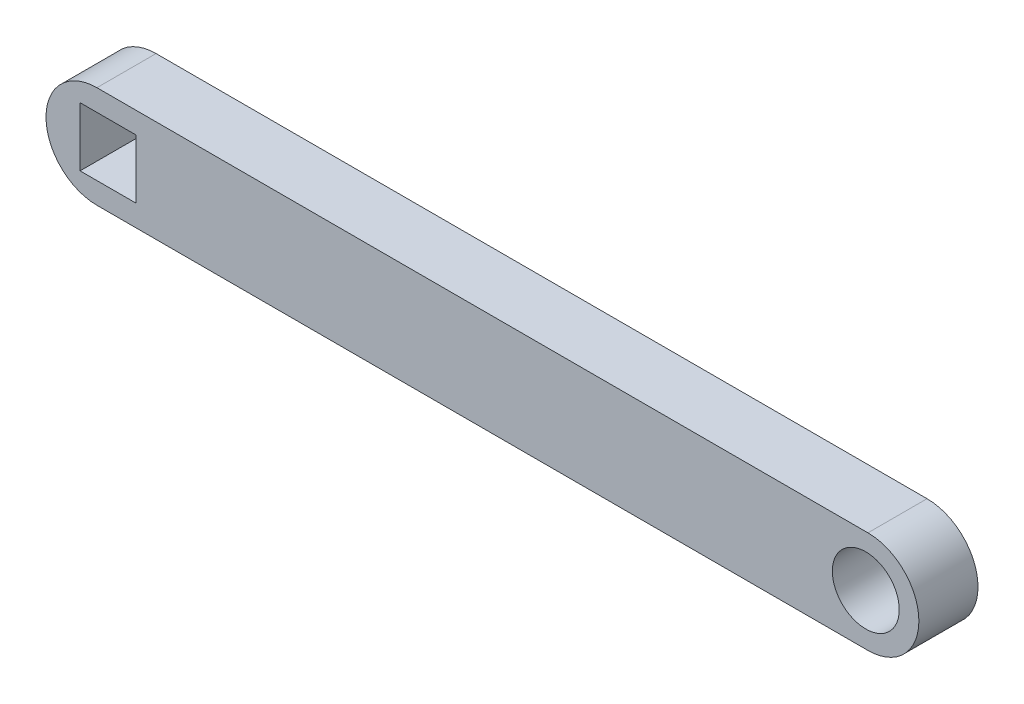
SolidWorks part; units mm, degrees
ref_plane "Front Plane" through (0, 0, 0) normal (0, 0, 1) x (1, 0, 0)
ref_plane "Top Plane" through (0, 0, 0) normal (0, 1, 0) x (1, 0, 0)
ref_plane "Right Plane" through (0, 0, 0) normal (1, 0, 0) x (0, 0, -1)
sketch "Sketch1" plane through (0, 0, 0) normal (0, 0, 1) x (1, 0, 0)
  line L0 (-43.5994, 0) -> (47.681, 0) construction
  line L1 (-43.5994, 6.0297) -> (47.681, 6.0297)
  line L2 (-43.5994, -6.0297) -> (47.681, -6.0297)
  arc A0 (-43.5994, 6.0297) -> (-43.5994, -6.0297) centre (-43.5994, 0) ccw
  arc A1 (47.681, -6.0297) -> (47.681, 6.0297) centre (47.681, 0) ccw
  point P3 (2.0408, 0)
  dimension "D1" = 12.0594
  dimension "D2" = 91.2804
extrude "Boss-Extrude1" add sketch "Sketch1" along normal mid plane 7
sketch "Sketch3" plane through (0, 0, 0) normal (0, 0, 1) x (1, 0, 0)
  circle A0 centre (47.4245, 0) radius 3.9607
extrude "Cut-Extrude2" cut sketch "Sketch3" against normal through all both and the other way through all
sketch "Sketch4" plane through (0, 0, 0) normal (0, 0, 1) x (1, 0, 0)
  line L1 (-38.9586, -3.4956) -> (-45.5943, -3.4956)
  line L2 (-38.9586, -3.4956) -> (-38.9586, 3.4956)
  line L3 (-38.9586, 3.4956) -> (-45.5943, 3.4956)
  line L4 (-45.5943, -3.4956) -> (-45.5943, 3.4956)
  line L5 (-38.9586, -3.4956) -> (-45.5943, 3.4956) construction
  line L6 (-38.9586, 3.4956) -> (-45.5943, -3.4956) construction
  point P0 (-42.2764, 0)
extrude "Cut-Extrude3" cut sketch "Sketch4" against normal through all both and the other way through all
sketch "Sketch5" plane through (0, 0, 0) normal (0, 0, 1) x (1, 0, 0)
  line L0 (-31.0194, 0) -> (36.286, 0) construction
  line L1 (-31.0194, 2.6661) -> (36.286, 2.6661)
  line L2 (-31.0194, -2.6661) -> (36.286, -2.6661)
  arc A0 (-31.0194, 2.6661) -> (-31.0194, -2.6661) centre (-31.0194, 0) ccw
  arc A1 (36.286, -2.6661) -> (36.286, 2.6661) centre (36.286, 0) ccw
  point P3 (2.6333, 0)
  dimension "D1" = 5.3323
  dimension "D2" = 67.3053
extrude "Boss-Extrude5" add sketch "Sketch5" against normal offset from surface (2 mm away) 5 from surface at 3.5 separate body up to face at (-42.2764, 0, -3.5) starting at face at (-42.2764, 0, 3.5)
